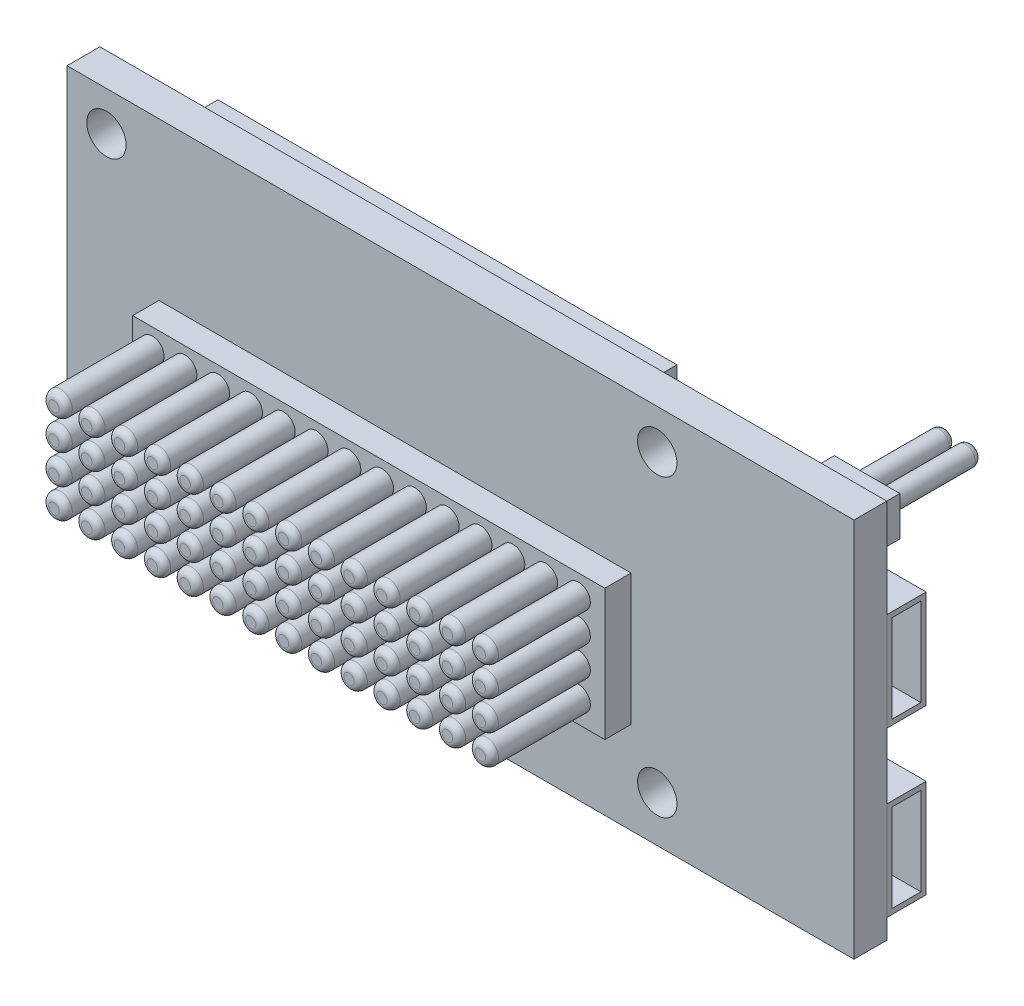
SolidWorks part; units mm, degrees
ref_plane "Ebene vorne" through (0, 0, 0) normal (0, 0, 1) x (1, 0, 0)
ref_plane "Ebene oben" through (0, 0, 0) normal (0, 1, 0) x (1, 0, 0)
ref_plane "Ebene rechts" through (0, 0, 0) normal (1, 0, 0) x (0, 0, -1)
sketch "Skizze1" plane through (0, 0, 0) normal (0, 0, 1) x (1, 0, 0)
  line L1 (-30, -14.5) -> (30, -14.5)
  line L2 (-30, -14.5) -> (-30, 14.5)
  line L3 (-30, 14.5) -> (30, 14.5)
  line L4 (30, -14.5) -> (30, 14.5)
  line L5 (-30, -14.5) -> (30, 14.5) construction
  line L6 (-30, 14.5) -> (30, -14.5) construction
  point P0 (0, 0)
  dimension "D1" = 60
  dimension "D2" = 29
extrude "Aufsatz-Linear austragen1" add sketch "Skizze1" along normal blind 2.5
sketch "Skizze2" plane through (0, 0, 2.5) normal (0, 0, 1) x (1, 0, 0)
  line L0 (-30, 14.5) -> (-30, -14.5) construction
  line L1 (30, 14.5) -> (-30, 14.5) construction
  circle A0 centre (-27, 11.5) radius 1.5
  circle A1 centre (15, 11.5) radius 1.5
  circle A2 centre (-27, -11) radius 1.5
  circle A3 centre (15, -11) radius 1.5
  dimension "D1" = 3
  dimension "D4" = 2
  dimension "D2" = 3
  dimension "D3" = 3
  dimension "D6" = 42
  dimension "D5" = 2
extrude "Schnitt-Linear austragen1" cut sketch "Skizze2" against normal through all
sketch "Skizze3" plane through (0, 0, 2.5) normal (0, 0, 1) x (1, 0, 0)
  line L0 (-30, -14.5) -> (30, -14.5) construction
  line L1 (13, 2.5) -> (-23, 2.5)
  line L2 (13, 2.5) -> (13, -7.5)
  line L3 (13, -7.5) -> (-23, -7.5)
  line L4 (-23, 2.5) -> (-23, -7.5)
  line L5 (13, 2.5) -> (-23, -7.5) construction
  line L6 (13, -7.5) -> (-23, 2.5) construction
  line L7 (-30, 14.5) -> (-30, -14.5) construction
  point P0 (-5, -2.5)
  dimension "D1" = 36
  dimension "D2" = 10
  dimension "D3" = 7
  dimension "D4" = 7
extrude "Aufsatz-Linear austragen2" add sketch "Skizze3" along normal blind 2
sketch "Skizze4" plane through (0, 0, 4.5) normal (0, 0, 1) x (1, 0, 0)
  line L0 (-23, 2.5) -> (-23, -7.5) construction
  line L1 (13, 2.5) -> (-23, 2.5) construction
  circle A0 centre (-21.5, 1) radius 0.9
  circle A1 centre (-19, 1) radius 0.9
  circle A2 centre (-16.5, 1) radius 0.9
  circle A3 centre (-14, 1) radius 0.9
  circle A4 centre (-11.5, 1) radius 0.9
  circle A5 centre (-9, 1) radius 0.9
  circle A6 centre (-6.5, 1) radius 0.9
  circle A7 centre (-4, 1) radius 0.9
  circle A8 centre (-1.5, 1) radius 0.9
  circle A9 centre (1, 1) radius 0.9
  circle A10 centre (3.5, 1) radius 0.9
  circle A11 centre (6, 1) radius 0.9
  circle A12 centre (8.5, 1) radius 0.9
  circle A13 centre (11, 1) radius 0.9
  circle A14 centre (-21.5, -1.25) radius 0.9
  circle A15 centre (-19, -1.25) radius 0.9
  circle A16 centre (-16.5, -1.25) radius 0.9
  circle A17 centre (-14, -1.25) radius 0.9
  circle A18 centre (-11.5, -1.25) radius 0.9
  circle A19 centre (-9, -1.25) radius 0.9
  circle A20 centre (-6.5, -1.25) radius 0.9
  circle A21 centre (-4, -1.25) radius 0.9
  circle A22 centre (-1.5, -1.25) radius 0.9
  circle A23 centre (1, -1.25) radius 0.9
  circle A24 centre (3.5, -1.25) radius 0.9
  circle A25 centre (6, -1.25) radius 0.9
  circle A26 centre (8.5, -1.25) radius 0.9
  circle A27 centre (11, -1.25) radius 0.9
  circle A28 centre (-21.5, -3.5) radius 0.9
  circle A29 centre (-19, -3.5) radius 0.9
  circle A30 centre (-16.5, -3.5) radius 0.9
  circle A31 centre (-14, -3.5) radius 0.9
  circle A32 centre (-11.5, -3.5) radius 0.9
  circle A33 centre (-9, -3.5) radius 0.9
  circle A34 centre (-6.5, -3.5) radius 0.9
  circle A35 centre (-4, -3.5) radius 0.9
  circle A36 centre (-1.5, -3.5) radius 0.9
  circle A37 centre (1, -3.5) radius 0.9
  circle A38 centre (3.5, -3.5) radius 0.9
  circle A39 centre (6, -3.5) radius 0.9
  circle A40 centre (8.5, -3.5) radius 0.9
  circle A41 centre (11, -3.5) radius 0.9
  circle A42 centre (-21.5, -5.75) radius 0.9
  circle A43 centre (-19, -5.75) radius 0.9
  circle A44 centre (-16.5, -5.75) radius 0.9
  circle A45 centre (-14, -5.75) radius 0.9
  circle A46 centre (-11.5, -5.75) radius 0.9
  circle A47 centre (-9, -5.75) radius 0.9
  circle A48 centre (-6.5, -5.75) radius 0.9
  circle A49 centre (-4, -5.75) radius 0.9
  circle A50 centre (-1.5, -5.75) radius 0.9
  circle A51 centre (1, -5.75) radius 0.9
  circle A52 centre (3.5, -5.75) radius 0.9
  circle A53 centre (6, -5.75) radius 0.9
  circle A54 centre (8.5, -5.75) radius 0.9
  circle A55 centre (11, -5.75) radius 0.9
  dimension "D1" = 1.8
  dimension "D2" = 1.5
  dimension "D3" = 1.5
  dimension "D4" = 14
  dimension "D5" = 4
extrude "Aufsatz-Linear austragen3" add sketch "Skizze4" along normal blind 7.5
fillet "Verrundung1" radius 0.5 56 edges at (-20.6, -5.75, 12) (-18.1, -5.75, 12) (-18.1, -3.5, 12) (-20.6, -3.5, 12) (-20.6, -1.25, 12) (-18.1, -1.25, 12) (-15.6, -1.25, 12) (-15.6, -3.5, 12) (-15.6, -5.75, 12) (-13.1, -5.75, 12) (-13.1, -3.5, 12) (-13.1, -1.25, 12) (-10.6, -1.25, 12) (-10.6, -3.5, 12) (-10.6, -5.75, 12) (-8.1, -5.75, 12) (-8.1, -3.5, 12) (-8.1, -1.25, 12) (-5.6, -1.25, 12) (-5.6, -3.5, 12) (-5.6, -5.75, 12) (-3.1, -5.75, 12) (-3.1, -3.5, 12) (-3.1, -1.25, 12) (-0.6, -1.25, 12) (-0.6, -3.5, 12) (-0.6, -5.75, 12) (1.9, -5.75, 12) (1.9, -3.5, 12) (1.9, -1.25, 12) (4.4, -1.25, 12) (4.4, -3.5, 12) (4.4, -5.75, 12) (6.9, -5.75, 12) (6.9, -3.5, 12) (6.9, -1.25, 12) (9.4, -1.25, 12) (9.4, -3.5, 12) (9.4, -5.75, 12) (11.9, -5.75, 12) (11.9, -3.5, 12) (11.9, -1.25, 12) (11.9, 1, 12) (9.4, 1, 12) (6.9, 1, 12) (4.4, 1, 12) (1.9, 1, 12) (-0.6, 1, 12) (-3.1, 1, 12) (-5.6, 1, 12) (-8.1, 1, 12) (-10.6, 1, 12) (-13.1, 1, 12) (-15.6, 1, 12) (-18.1, 1, 12) (-20.6, 1, 12)
sketch "Skizze5" plane through (0, 0, 0) normal (0, 0, -1) x (-1, 0, 0)
  line L0 (30, -14.5) -> (-30, -14.5) construction
  line L1 (-11, -12.5) -> (24, -12.5)
  line L2 (-11, -12.5) -> (-11, 12.5)
  line L3 (-11, 12.5) -> (24, 12.5)
  line L4 (24, -12.5) -> (24, 12.5)
  line L5 (30, 14.5) -> (30, -14.5) construction
  dimension "D1" = 35
  dimension "D2" = 25
  dimension "D3" = 2
  dimension "D4" = 6
extrude "Aufsatz-Linear austragen4" add sketch "Skizze5" along normal blind 3
sketch "Skizze6" plane through (0, 0, -3) normal (0, 0, -1) x (-1, 0, 0)
  line L0 (24, 12.5) -> (-11, 12.5) construction
  line L1 (-11, -12.5) -> (16, -12.5)
  line L2 (-11, -12.5) -> (-11, 6.5)
  line L3 (-11, 6.5) -> (16, 6.5)
  line L4 (16, -12.5) -> (16, 6.5)
  line L5 (24, -12.5) -> (24, 12.5) construction
  dimension "D1" = 6
  dimension "D2" = 8
extrude "Aufsatz-Linear austragen5" add sketch "Skizze6" along normal blind 2
sketch "Skizze8" plane through (0, 0, -5) normal (0, 0, -1) x (-1, 0, 0)
  line L0 (-11, 6.5) -> (-11, -12.5) construction
  text T0 "intel´" font "Corbel" height 3.5
  text T1 "Edison" font "Arial Narrow" height 3.5
  text T2 "What will you make?" font "Century Gothic" height in points 6
  dimension "D2" = 2.5
extrude "Aufsatz-Linear austragen6" add sketch "Skizze8" along normal blind 0.1 separate body
sketch "Skizze9" plane through (0, 0, -5) normal (0, 0, -1) x (-1, 0, 0)
  ellipse E0 centre (-3.1043, 1.0887) end of major axis (-9.0573, -0.6697) minor radius 3.4109
  ellipse E1 centre (-3.1043, 1.0887) end of major axis (-8.8573, -0.6697) minor radius 3.4389
  point P1 (0, 0)
  point P12 (0, 0)
  line M1 (-11, 6.5) -> (-11, -12.5)
  dimension "D1" = 0.2
  dimension "D2" = 0.2
extrude "Schnitt-Linear austragen3" cut sketch "Skizze9" against normal blind 0.1 contours E0 E1 M1
sketch "Skizze10" plane through (0, 0, 0) normal (0, 0, -1) x (-1, 0, 0)
  line L0 (-30, -14.5) -> (-30, 14.5) construction
  line L1 (-30, -5.5) -> (-24, -5.5)
  line L2 (-30, -5.5) -> (-30, -13)
  line L3 (-30, -13) -> (-24, -13)
  line L4 (-24, -5.5) -> (-24, -13)
  line L5 (30, -14.5) -> (-30, -14.5) construction
  dimension "D1" = 7.5
  dimension "D2" = 6
  dimension "D3" = 1.5
extrude "Aufsatz-Linear austragen8" add sketch "Skizze10" along normal blind 3 separate body
pattern_linear "Lineares Muster1" count 2 spacing 12.5 along (0, 1, 0) of "Aufsatz-Linear austragen8"
shell "Wandung1" thickness 0.4
shell "Wandung2" thickness 0.4
sketch "Skizze11" plane through (0, 0, 0) normal (0, 0, -1) x (-1, 0, 0)
  line L0 (-30, 14.5) -> (30, 14.5) construction
  line L1 (-28.5, 13) -> (-23.5, 13)
  line L2 (-28.5, 13) -> (-28.5, 10)
  line L3 (-28.5, 10) -> (-23.5, 10)
  line L4 (-23.5, 13) -> (-23.5, 10)
  line L5 (-30, -14.5) -> (-30, 14.5) construction
  dimension "D1" = 5
  dimension "D2" = 3
  dimension "D3" = 1.5
  dimension "D4" = 1.5
extrude "Aufsatz-Linear austragen9" add sketch "Skizze11" along normal blind 2.5
sketch "Skizze12" plane through (0, 0, -2.5) normal (0, 0, -1) x (-1, 0, 0)
  line L0 (-28.5, 13) -> (-28.5, 10) construction
  line L1 (-23.5, 10) -> (-23.5, 13) construction
  line L2 (-23.5, 13) -> (-28.5, 13) construction
  circle A0 centre (-27, 11.5) radius 0.75
  circle A2 centre (-25, 11.5) radius 0.75
  dimension "D1" = 1.5
  dimension "D5" = 1.5
  dimension "D2" = 1.5
  dimension "D4" = 1.5
  dimension "D6" = 1.5
  dimension "D3" = 0
extrude "Aufsatz-Linear austragen11" add sketch "Skizze12" along normal blind 7
fillet "Verrundung3" radius 0.5 2 edges at (26.25, 11.5, -9.5) (24.25, 11.5, -9.5)
